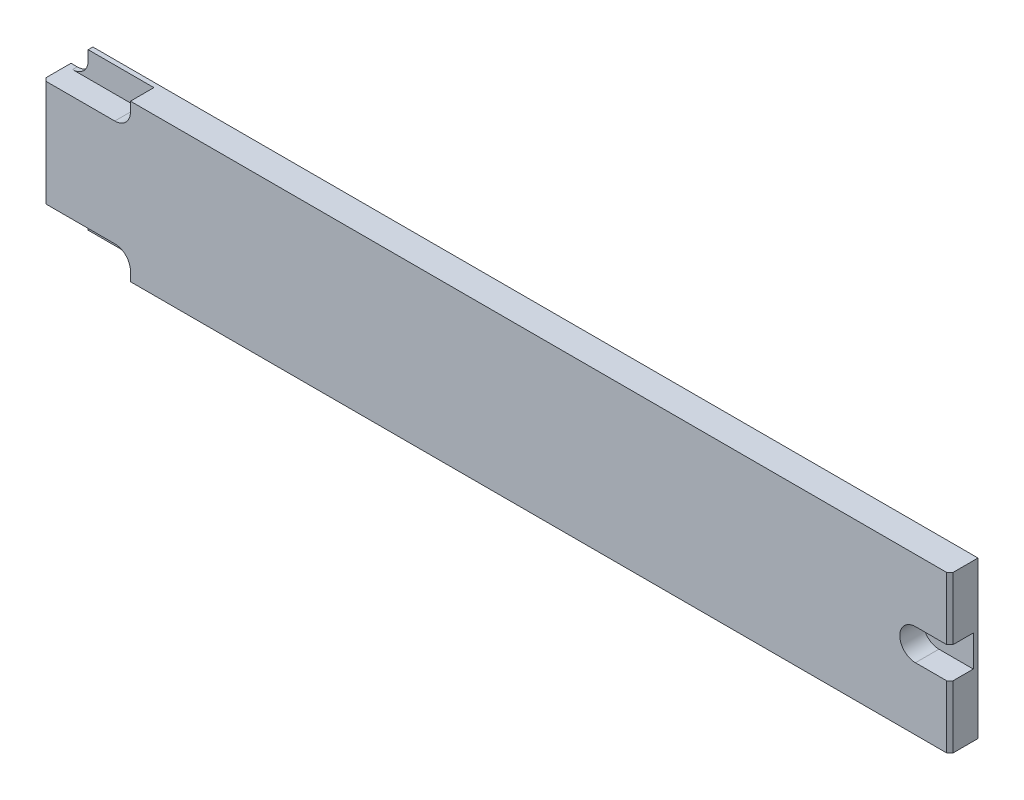
SolidWorks part; units mm, degrees
ref_plane "Plane1" through (0, 0, 0) normal (0, 0, 1) x (1, 0, 0)
ref_plane "Plane2" through (0, 0, 0) normal (0, 1, 0) x (1, 0, 0)
ref_plane "Plane3" through (0, 0, 0) normal (1, 0, 0) x (0, 0, -1)
sketch "Sketch1" plane through (0, 0, 0) normal (0, 0, 1) x (1, 0, 0)
  line L0 (7, 0) -> (290, 0)
  line L1 (0, 8) -> (0, 42)
  line L2 (290, 50) -> (7, 50)
  line L3 (290, 50) -> (290, 0)
  line L4 (0, 8) -> (2, 8)
  line L5 (7, 3) -> (7, 0)
  line L6 (7, 47) -> (7, 50)
  line L8 (-4.3217, 25) -> (290, 25) construction
  line L9 (0, 42) -> (2, 42)
  arc A1 (2, 8) -> (7, 3) centre (2, 3) cw
  arc A2 (2, 42) -> (7, 47) centre (2, 47) ccw
  dimension "D4" = 5
  dimension "D1" = 290
  dimension "D2" = 7
  dimension "D3" = 50
  dimension "D5" = 8
extrude "Base-Extrude" add sketch "Sketch1" along normal blind 9
sketch "Sketch2" plane through (0, 0, 9) normal (0, 0, 1) x (1, 0, 0)
  line L0 (0, 25) -> (290, 25) construction
  line L1 (7, 0) -> (290, 0) construction
  line L2 (2, 8) -> (23, 8)
  line L3 (290, 50) -> (290, 0) construction
  line L4 (145, 25) -> (145, -44) construction
  line L5 (2, 8) -> (2, 0)
  line L6 (290, 50) -> (290, 0) construction
  line L7 (28, 0) -> (2, 0)
  line L8 (290, 50) -> (290, 41) construction
  line L9 (290, 9) -> (281, 0) construction
  line L10 (290, 41) -> (281, 50) construction
  line L11 (290, 50) -> (7, 50) construction
  line L12 (290, 50) -> (281, 50) construction
  line L13 (290, 9) -> (290, 0) construction
  line L14 (281, 0) -> (290, 0) construction
  line L15 (28, 3) -> (28, 0)
  line L16 (7, 0) -> (290, 0) construction
  line L17 (279, 30) -> (290, 30)
  line L18 (279, 20) -> (290, 20)
  line L19 (290, 20) -> (290, 30)
  line L20 (28, 47) -> (28, 50)
  line L21 (28, 50) -> (2, 50)
  line L22 (2, 42) -> (2, 50)
  line L23 (2, 42) -> (23, 42)
  arc A0 (23, 8) -> (28, 3) centre (23, 3) cw
  arc A1 (279, 20) -> (279, 30) centre (279, 25) cw
  arc A3 (23, 42) -> (28, 47) centre (23, 47) ccw
  dimension "D4" = 26
  dimension "D1" = 5
  dimension "D5" = 5
  dimension "D2" = 45
  dimension "D3" = 9
  dimension "D6" = 11
extrude "Cut-Extrude1" cut sketch "Sketch2" against normal offset from surface (7.5 mm away) 1.5 up to face at (61.4071, 25, 0)
chamfer "Chamfer1" distance 1 angle 45 3 edges at (0, 25, 9) (290, 40, 9) (290, 10, 9)
